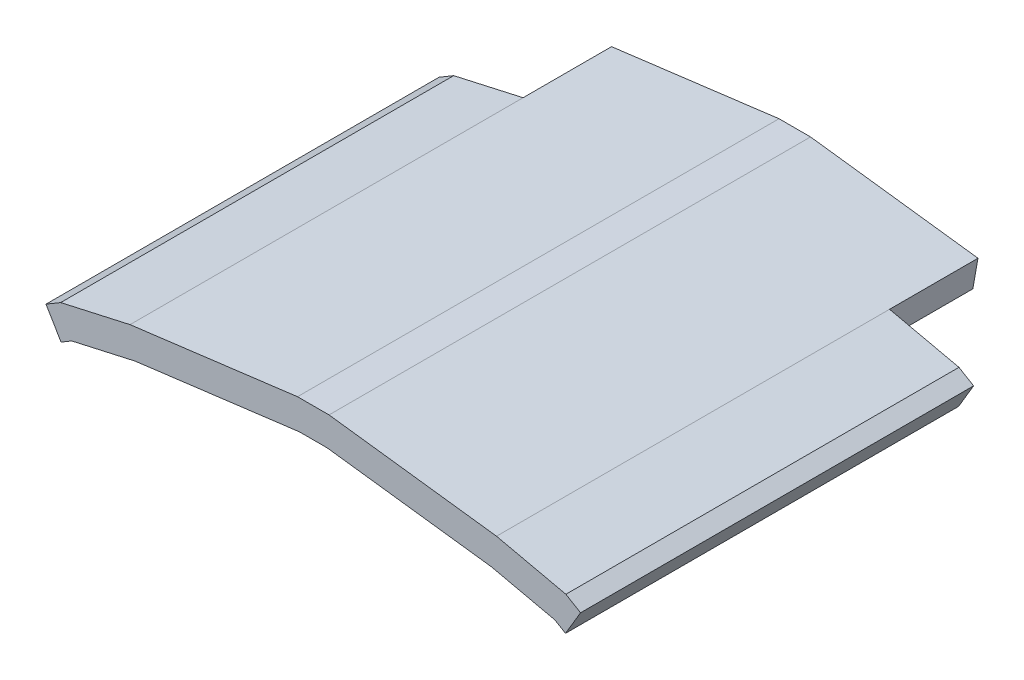
SolidWorks part; units mm, degrees
ref_plane "Front Plane" through (0, 0, 0) normal (0, 0, 1) x (1, 0, 0)
ref_plane "Top Plane" through (0, 0, 0) normal (0, 1, 0) x (1, 0, 0)
ref_plane "Right Plane" through (0, 0, 0) normal (1, 0, 0) x (0, 0, -1)
sketch "Sketch1" plane through (0, 0, 0) normal (0, 0, 1) x (1, 0, 0)
  line L0 (0, 0) -> (0, 18.4909) construction
  line L12 (0, 0) -> (34.544, 0) construction
  line L13 (-2.0378, 0) -> (2.0378, 0)
  line L24 (2.0378, 0) -> (4.9014, -0.3645)
  line L25 (4.9014, -0.3645) -> (9.5607, -0.9575)
  line L26 (9.5607, -0.9575) -> (23.6815, -2.7547)
  line L27 (23.6815, -2.7547) -> (32.6496, -4.7683)
  line L28 (32.6496, -4.7683) -> (34.544, -5.8924)
  line L29 (-32.6496, -4.7683) -> (-34.544, -5.8924)
  line L30 (-23.6815, -2.7547) -> (-32.6496, -4.7683)
  line L31 (-9.5607, -0.9575) -> (-23.6815, -2.7547)
  line L32 (-4.9014, -0.3645) -> (-9.5607, -0.9575)
  line L33 (-2.0378, 0) -> (-4.9014, -0.3645)
  line L34 (-31.2251, -8.3533) -> (-32.5997, -9.169)
  line L35 (-23.0222, -6.5115) -> (-31.2251, -8.3533)
  line L36 (-9.0797, -4.737) -> (-23.0222, -6.5115)
  line L37 (-4.4203, -4.144) -> (-9.0797, -4.737)
  line L38 (-1.7963, -3.81) -> (-4.4203, -4.144)
  line L39 (-1.7963, -3.81) -> (1.7963, -3.81)
  line L40 (1.7963, -3.81) -> (4.4203, -4.144)
  line L41 (4.4203, -4.144) -> (9.0797, -4.737)
  line L42 (9.0797, -4.737) -> (23.0222, -6.5115)
  line L43 (23.0222, -6.5115) -> (31.2251, -8.3533)
  line L44 (31.2251, -8.3533) -> (32.5997, -9.169)
  line L45 (-34.544, -5.8924) -> (-32.5997, -9.169)
  line L46 (34.544, -5.8924) -> (32.5997, -9.169)
  dimension "D1" = 34.544
  dimension "D2" = 3.81
extrude "Boss-Extrude1" add sketch "Sketch1" along normal blind 50.8
sketch "Sketch2" plane through (0, 0, 0) normal (0, 0, -1) x (-1, 0, 0)
  line L0 (23.0222, -6.5115) -> (1.7963, -3.81) construction
  line L1 (2.0378, 0) -> (23.6815, -2.7547) construction
  line L2 (-1.7963, -3.81) -> (-23.0222, -6.5115) construction
  line L3 (-23.6815, -2.7547) -> (-2.0378, 0) construction
  line L4 (1.7963, -3.81) -> (-1.7963, -3.81) construction
  line L5 (-2.0378, 0) -> (2.0378, 0) construction
  line L6 (23.0222, -6.5115) -> (1.7963, -3.81)
  line L7 (2.0378, 0) -> (23.6815, -2.7547)
  line L8 (-1.7963, -3.81) -> (-23.0222, -6.5115)
  line L9 (-23.6815, -2.7547) -> (-2.0378, 0)
  line L10 (1.7963, -3.81) -> (-1.7963, -3.81)
  line L11 (-2.0378, 0) -> (2.0378, 0)
  line L12 (-23.6815, -2.7547) -> (-23.0222, -6.5115)
  line L13 (23.6815, -2.7547) -> (23.0222, -6.5115)
extrude "Boss-Extrude2" add sketch "Sketch2" along normal blind 11.43
